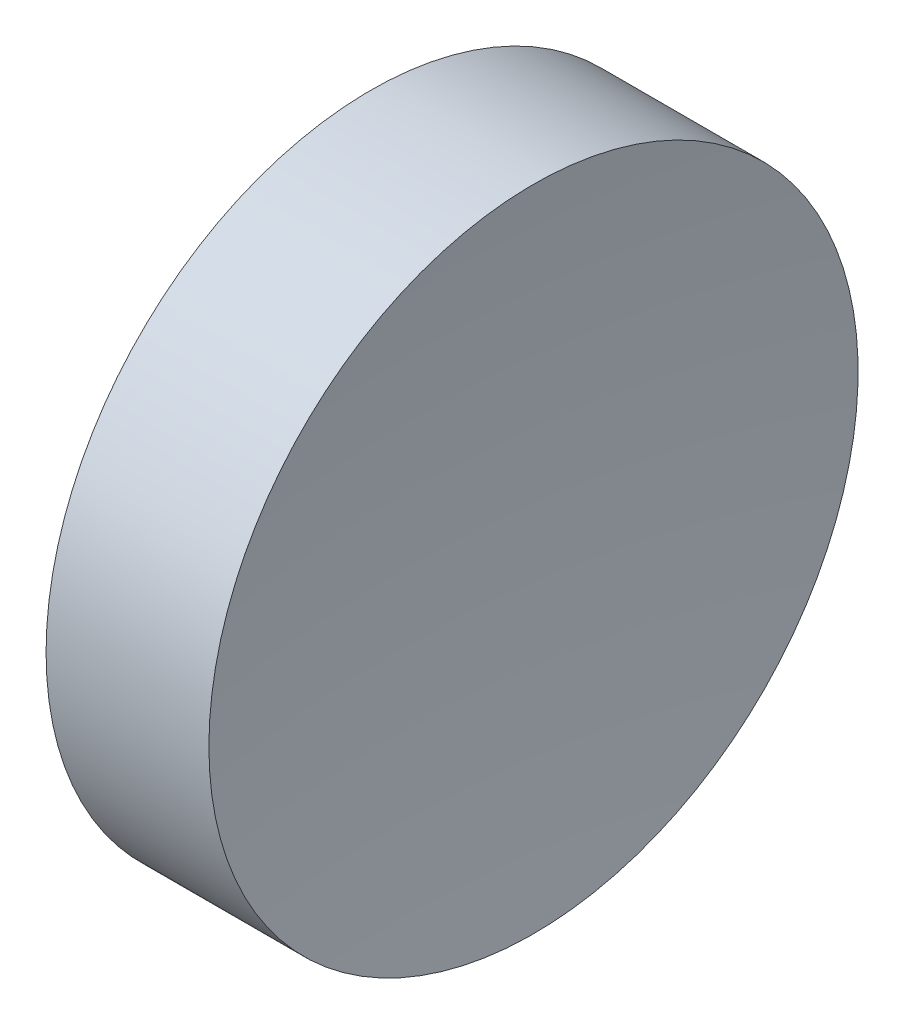
SolidWorks part; units mm, degrees
ref_plane "前视基准面" through (0, 0, 0) normal (0, 0, 1) x (1, 0, 0)
ref_plane "上视基准面" through (0, 0, 0) normal (0, 1, 0) x (1, 0, 0)
ref_plane "右视基准面" through (0, 0, 0) normal (1, 0, 0) x (0, 0, -1)
sketch "草图1" plane through (0, 0, 0) normal (0, 1, 0) x (1, 0, 0)
  line L0 (0, 0) -> (6.9328, 0) construction
  line L1 (0, 0) -> (2.78, 0)
  line L2 (0, 0) -> (0, 6.35)
  line L3 (0, 6.35) -> (3.1849, 6.35)
  arc A0 (3.1849, 6.35) -> (2.78, 0) centre (52.78, 0) ccw
  dimension "D3" = 50
  dimension "D1" = 2.78
  dimension "D2" = 6.35
revolve "旋转1" add sketch "草图1" angle 360 about L0
